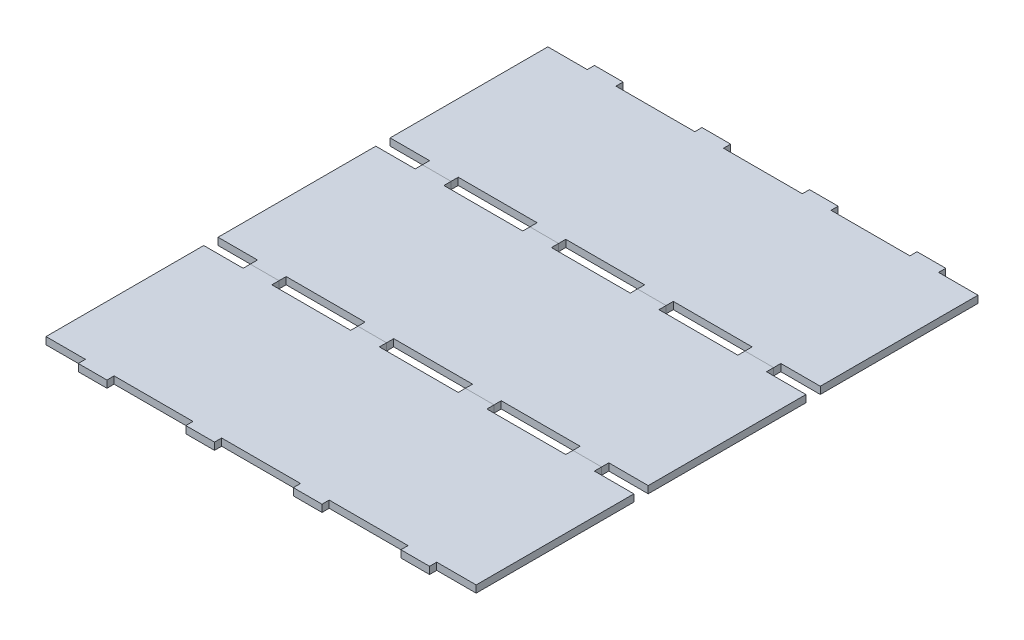
SolidWorks part; units mm, degrees
material "Cedar"
ref_plane "Front Plane" through (0, 0, 0) normal (0, 0, 1) x (1, 0, 0)
ref_plane "Top Plane" through (0, 0, 0) normal (0, 1, 0) x (1, 0, 0)
ref_plane "Right Plane" through (0, 0, 0) normal (1, 0, 0) x (0, 0, -1)
sketch "Sketch1" plane through (0, 0, 0) normal (0, 1, 0) x (1, 0, 0)
  line L1 (-190.5, 76.2) -> (190.5, 76.2)
  line L2 (-190.5, 76.2) -> (-190.5, -76.2)
  line L3 (-190.5, -76.2) -> (190.5, -76.2)
  line L4 (190.5, 76.2) -> (190.5, -76.2)
  line L5 (-190.5, 76.2) -> (190.5, -76.2) construction
  line L6 (-190.5, -76.2) -> (190.5, 76.2) construction
  point P0 (0, 0)
  dimension "D1" = 152.4
  dimension "D2" = 381
extrude "Boss-Extrude1" add sketch "Sketch1" along normal blind 6.35
sketch "Sketch2" plane through (0, 6.35, 0) normal (0, 1, 0) x (1, 0, 0)
  line L0 (-190.5, -69.85) -> (190.5, -69.85) construction
  line L1 (-190.5, 76.2) -> (-190.5, -76.2) construction
  line L2 (190.5, -76.2) -> (190.5, 76.2) construction
  line L3 (-190.5, -76.2) -> (190.5, -76.2) construction
  line L5 (-34.925, -69.85) -> (34.925, -69.85)
  line L6 (-34.925, -69.85) -> (-34.925, -76.2)
  line L7 (-34.925, -76.2) -> (34.925, -76.2)
  line L8 (34.925, -69.85) -> (34.925, -76.2)
  line L9 (-34.925, -69.85) -> (34.925, -76.2) construction
  line L10 (-34.925, -76.2) -> (34.925, -69.85) construction
  point P8 (0, -73.025)
  point P14 (0, -69.85)
  point P18 (0, -69.85)
  dimension "D1" = 6.35
  dimension "D2" = 69.85
extrude "Cut-Extrude2" cut sketch "Sketch2" against normal through all
pattern_linear "LPattern1" count 3 spacing 95.25 along (-1, 0, 0) count 3 spacing 95.25 along (1, 0, 0) of "Cut-Extrude2"
mirror "Mirror2" about plane through (0, 0, 0) normal (0, 0, 1) of "LPattern1", "Cut-Extrude2"
pattern_linear "LPattern2" count 3 spacing 152.4 along (0, 0, 1) of bodies 106
